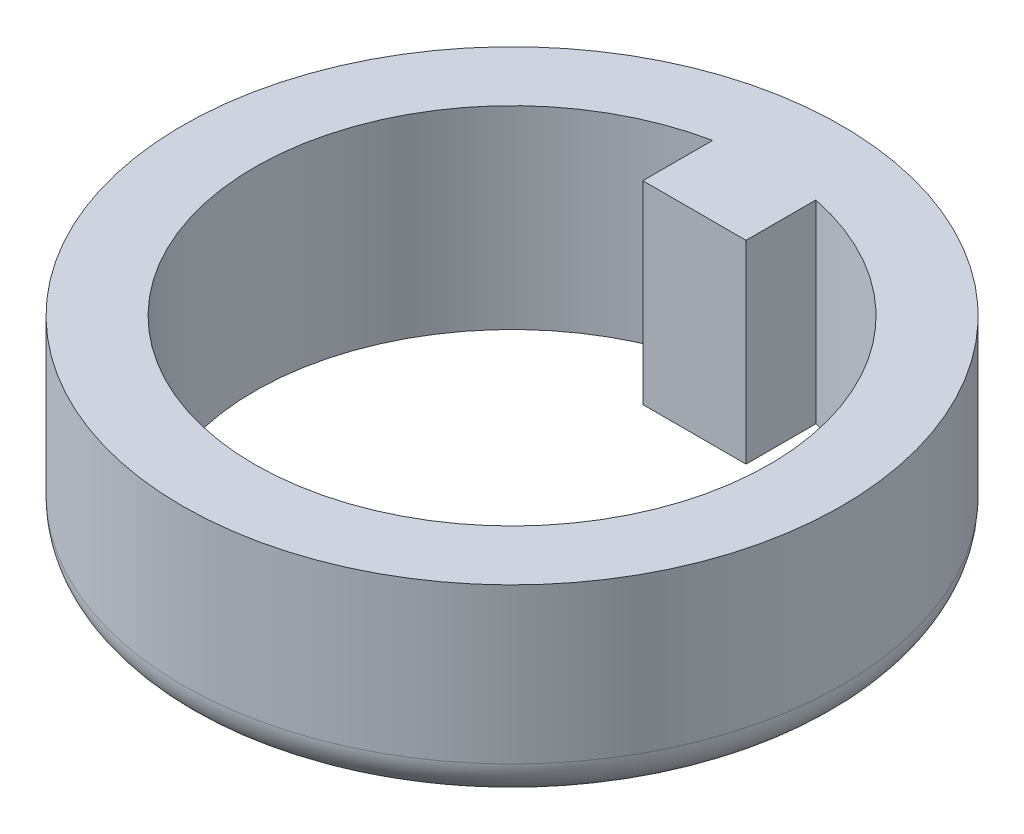
SolidWorks part; units mm, degrees
ref_plane "Front Plane" through (0, 0, 0) normal (0, 0, 1) x (1, 0, 0)
ref_plane "Top Plane" through (0, 0, 0) normal (0, 1, 0) x (1, 0, 0)
ref_plane "Right Plane" through (0, 0, 0) normal (1, 0, 0) x (0, 0, -1)
sketch "Sketch1" plane through (0, 0, 0) normal (0, 1, 0) x (1, 0, 0)
  line L0 (-1.332, 6.504) -> (-1.332, 4.704)
  line L1 (-1.332, 4.704) -> (1.33, 4.704)
  line L2 (1.33, 4.704) -> (1.33, 6.5044)
  circle A0 centre (0, 0) radius 8.5
  arc A1 (-1.332, 6.504) -> (1.33, 6.5044) centre (0, 0) ccw
  dimension "D1" = 13.278
  dimension "D2" = 17
  dimension "D3" = 1.8
  dimension "D4" = 2.662
  dimension "D5" = 1.33
extrude "Boss-Extrude1" add sketch "Sketch1" along normal blind 5
fillet "Fillet3" radius 1 1 edges at (0, 0, 8.5)
